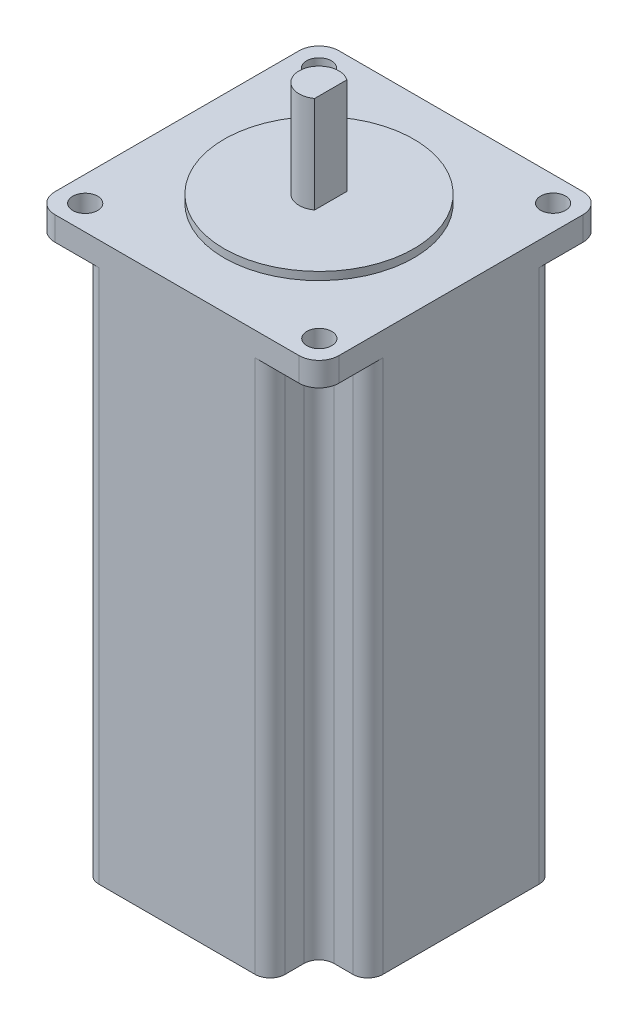
SolidWorks part; units mm, degrees
ref_plane "Front Plane" through (0, 0, 0) normal (0, 0, 1) x (1, 0, 0)
ref_plane "Top Plane" through (0, 0, 0) normal (0, 1, 0) x (1, 0, 0)
ref_plane "Right Plane" through (0, 0, 0) normal (1, 0, 0) x (0, 0, -1)
sketch "Sketch1" plane through (0, 0, 0) normal (0, 1, 0) x (1, 0, 0)
  line L1 (-24.5, -28.5) -> (24.5, -28.5)
  line L2 (-28.5, -24.5) -> (-28.5, 24.5)
  line L3 (-24.5, 28.5) -> (24.5, 28.5)
  line L4 (28.5, -24.5) -> (28.5, 24.5)
  line L5 (-28.5, -28.5) -> (28.5, 28.5) construction
  line L6 (-28.5, 28.5) -> (28.5, -28.5) construction
  arc A0 (-24.5, -28.5) -> (-28.5, -24.5) centre (-24.5, -24.5) cw
  arc A1 (24.5, -28.5) -> (28.5, -24.5) centre (24.5, -24.5) ccw
  arc A2 (24.5, 28.5) -> (28.5, 24.5) centre (24.5, 24.5) cw
  arc A3 (-24.5, 28.5) -> (-28.5, 24.5) centre (-24.5, 24.5) ccw
  point P0 (0, 0)
  dimension "D3" = 4
  dimension "D1" = 57
  dimension "D2" = 57
extrude "Boss-Extrude1" add sketch "Sketch1" along normal blind 112
sketch "Sketch2" plane through (0, 112, 0) normal (0, 1, 0) x (1, 0, 0)
  circle A0 centre (0, 0) radius 19.05
  dimension "D1" = 38.1
extrude "Boss-Extrude2" add sketch "Sketch2" along normal blind 1.6
sketch "Sketch3" plane through (0, 113.6, 0) normal (0, 1, 0) x (1, 0, 0)
  circle A0 centre (0, 0) radius 4
  dimension "D1" = 8
extrude "Boss-Extrude3" add sketch "Sketch3" along normal blind 19.4
sketch "Sketch4" plane through (0, 133, 0) normal (0, 1, 0) x (1, 0, 0)
  line L1 (2.3563, 3.7394) -> (10.2524, 3.7394)
  line L2 (2.3563, 3.7394) -> (2.3563, -3.5855)
  line L3 (2.3563, -3.5855) -> (10.2524, -3.5855)
  line L4 (10.2524, 3.7394) -> (10.2524, -3.5855)
extrude "Cut-Extrude1" cut sketch "Sketch4" against normal blind 19.4 contours L2 L1 L4 L3
sketch "Sketch5" plane through (0, 0, 0) normal (0, -1, 0) x (1, 0, 0)
  line L1 (-28.5, -28.5) -> (28.5, -28.5)
  line L2 (-28.5, -28.5) -> (-28.5, 28.5)
  line L3 (-28.5, 28.5) -> (28.5, 28.5)
  line L4 (28.5, -28.5) -> (28.5, 28.5)
  line L5 (-28.5, -28.5) -> (28.5, 28.5) construction
  line L6 (-28.5, 28.5) -> (28.5, -28.5) construction
  line L7 (-28.5, 28.5) -> (-18.6831, 28.5)
  line L8 (-28.5, 28.5) -> (-28.5, 18.6831)
  line L9 (-28.5, 18.6831) -> (-18.6831, 18.6831)
  line L10 (-18.6831, 28.5) -> (-18.6831, 18.6831)
  line L11 (28.5, 28.5) -> (19.6135, 28.5)
  line L12 (28.5, 28.5) -> (28.5, 19.6135)
  line L13 (28.5, 19.6135) -> (19.6135, 19.6135)
  line L14 (19.6135, 28.5) -> (19.6135, 19.6135)
  line L15 (28.5, -28.5) -> (18.6831, -28.5)
  line L16 (28.5, -28.5) -> (28.5, -18.6831)
  line L17 (28.5, -18.6831) -> (18.6831, -18.6831)
  line L18 (18.6831, -28.5) -> (18.6831, -18.6831)
  line L19 (-28.5, -28.5) -> (-18.6831, -28.5)
  line L20 (-28.5, -28.5) -> (-28.5, -18.6831)
  line L21 (-28.5, -18.6831) -> (-18.6831, -18.6831)
  line L22 (-18.6831, -28.5) -> (-18.6831, -18.6831)
  point P0 (0, 0)
  arc M19 (-24.5, 28.5) -> (-28.5, 24.5) centre (-24.5, 24.5) ccw
  line M20 (-28.5, 24.5) -> (-28.5, -24.5)
extrude "Cut-Extrude2" cut sketch "Sketch5" against normal blind 107.2 contours L10 L3 L9 M19 M20
mirror "Mirror1" about plane through (0, 0, 0) normal (1, 0, 0) of "Cut-Extrude2"
mirror "Mirror2" about plane through (0, 0, 0) normal (0, 0, 1) of "Mirror1", "Cut-Extrude2"
fillet "Fillet1" radius 3 12 edges at (-18.6831, 53.6, -18.6831) (-18.6831, 53.6, 18.6831) (18.6831, 53.6, 18.6831) (28.5, 53.6, -18.6831) (18.6831, 53.6, -18.6831) (18.6831, 53.6, -28.5) (-18.6831, 53.6, -28.5) (-28.5, 53.6, -18.6831) (-18.6831, 53.6, 28.5) (-28.5, 53.6, 18.6831) (28.5, 53.6, 18.6831) (18.6831, 53.6, 28.5)
sketch "Sketch6" plane through (0, 112, 0) normal (0, 1, 0) x (1, 0, 0)
  circle A0 centre (23.5, 23.5) radius 2.5
  circle A1 centre (23.5644, -23.5) radius 2.5
  circle A2 centre (-23.5, 23.5) radius 2.5
  circle A3 centre (-23.4356, -23.5) radius 2.5
  dimension "D8" = 5
  dimension "D9" = 5
  dimension "D10" = 5
  dimension "D11" = 5
  dimension "D1" = 47
  dimension "D2" = 23.5
  dimension "D3" = 47
  dimension "D4" = 47
  dimension "D5" = 47
  dimension "D6" = 23.5
  dimension "D7" = 23.5
extrude "Cut-Extrude3" cut sketch "Sketch6" against normal blind 107.2
